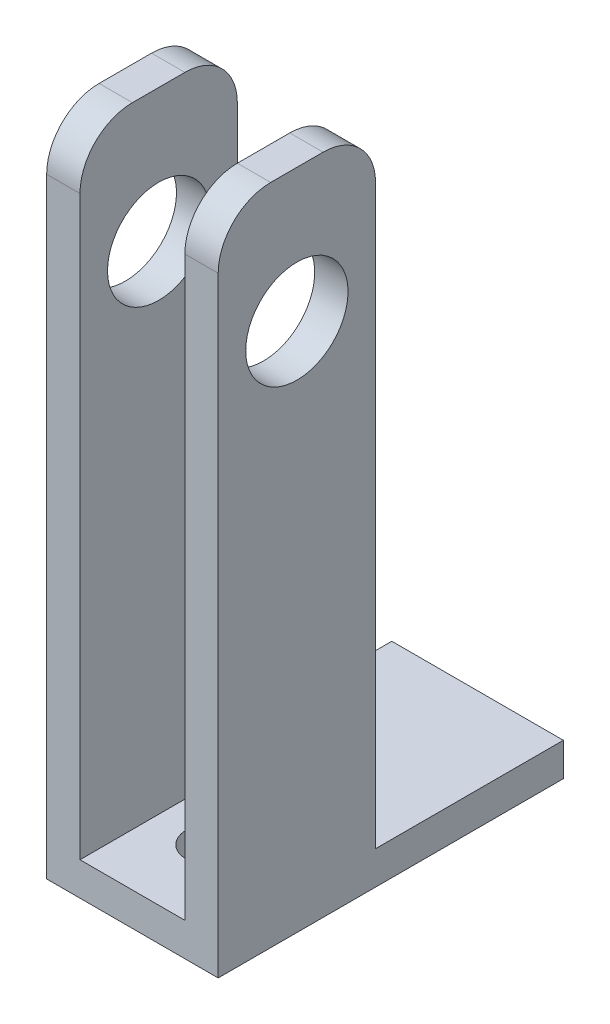
SolidWorks part; units mm, degrees
ref_plane "Front Plane" through (0, 0, 0) normal (0, 0, 1) x (1, 0, 0)
ref_plane "Top Plane" through (0, 0, 0) normal (0, 1, 0) x (1, 0, 0)
ref_plane "Right Plane" through (0, 0, 0) normal (1, 0, 0) x (0, 0, -1)
sketch "Sketch1" plane through (0, 0, 0) normal (0, 1, 0) x (1, 0, 0)
  circle A0 centre (0, 0) radius 10
  dimension "D1" = 20
extrude "Boss-Extrude1" add sketch "Sketch1" along normal blind 6.35
sketch "Sketch5" plane through (0, 6.35, 0) normal (0, 1, 0) x (1, 0, 0)
  line L27 (0, 15) -> (0, -15) construction
  line L28 (-10, 15) -> (10, 15)
  line L29 (-10, 15) -> (-10, -15)
  line L30 (-10, -15) -> (10, -15)
  line L31 (10, 15) -> (10, -15)
  line L32 (-10, 0) -> (10, 0) construction
  point P0 (0, 0)
  dimension "D1" = 20
  dimension "D2" = 30
extrude "Boss-Extrude2" add sketch "Sketch5" against normal blind 6.35
sketch "Sketch7" plane through (0, 6.35, 0) normal (0, 1, 0) x (1, 0, 0)
  line L13 (0, 0) -> (0, 21) construction
  line L29 (-16.35, 15) -> (-10, 15)
  line L30 (-16.35, 15) -> (-16.35, -15)
  line L31 (-16.35, -15) -> (-10, -15)
  line L32 (-10, 15) -> (-10, -15)
  line L38 (10, 15) -> (10, -15)
  line L39 (16.35, -15) -> (10, -15)
  line L40 (16.35, 15) -> (16.35, -15)
  line L41 (16.35, 15) -> (10, 15)
  circle A0 centre (0, 0) radius 38 construction
  dimension "D1" = 6.35
  dimension "D2" = 30
extrude "Boss-Extrude3" add sketch "Sketch7" along normal blind 120 and the other way blind 6.35
sketch "Sketch8" plane through (-16.35, 0, 0) normal (-1, 0, 0) x (0, 0, 1)
  line L0 (-15, 0) -> (15, 0) construction
  line L4 (-15, 126.35) -> (15, 126.35) construction
  line L5 (0, 126.35) -> (0, 0) construction
  line L6 (-15, 126.35) -> (15, 126.35) construction
  line L7 (-15, 0) -> (15, 0) construction
  circle A0 centre (0, 100.95) radius 9.75
  dimension "D1" = 19.5
  dimension "D2" = 25.4
extrude "Cut-Extrude2" cut sketch "Sketch8" against normal through all
sketch "Sketch2" plane through (0, 6.35, 0) normal (0, 1, 0) x (1, 0, 0)
  circle A0 centre (0, 0) radius 4.7625
  dimension "D1" = 9.525
extrude "Cut-Extrude1" cut sketch "Sketch2" against normal through all
fillet "Fillet2" radius 10 4 edges at (13.175, 126.35, -15) (-13.175, 126.35, 15) (13.175, 126.35, 15) (-13.175, 126.35, -15)
sketch "Sketch11" plane through (0, 0, 0) normal (0, -1, 0) x (1, 0, 0)
  line L1 (-16.35, -15) -> (16.35, -15)
  line L2 (-16.35, -15) -> (-16.35, -50.8)
  line L3 (-16.35, -50.8) -> (16.35, -50.8)
  line L4 (16.35, -15) -> (16.35, -50.8)
  dimension "D1" = 35.8
extrude "Boss-Extrude5" add sketch "Sketch11" against normal blind 6.35
